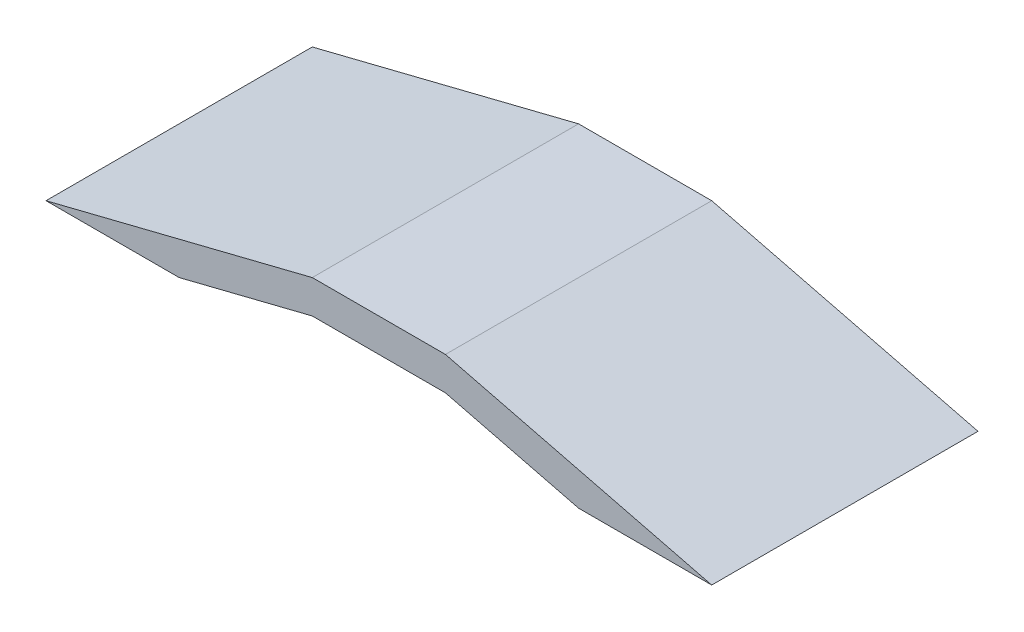
SolidWorks part; units mm, degrees
ref_plane "Front Plane" through (0, 0, 0) normal (0, 0, 1) x (1, 0, 0)
ref_plane "Top Plane" through (0, 0, 0) normal (0, 1, 0) x (1, 0, 0)
ref_plane "Right Plane" through (0, 0, 0) normal (1, 0, 0) x (0, 0, -1)
sketch "Sketch1" plane through (0, 0, 0) normal (0, 0, 1) x (1, 0, 0)
  line L0 (0, 0) -> (2000, 0)
  line L1 (2000, 0) -> (0, 500)
  line L2 (0, 500) -> (0, 0)
  line L3 (-500, 500) -> (-500, 0) construction
  line L4 (0, 0) -> (-1000, 0)
  line L5 (0, 0) -> (0, 500)
  line L6 (0, 500) -> (-1000, 500)
  line L7 (-1000, 0) -> (-1000, 500)
  line L8 (-1000, 0) -> (-3000, 0)
  line L9 (-1000, 500) -> (-1000, 0)
  line L10 (-3000, 0) -> (-1000, 500)
  line L11 (-2000, 0) -> (-1000, 250)
  line L12 (-1000, 250) -> (0, 250)
  line L13 (0, 250) -> (1000, 0)
  dimension "D1" = 2000
  dimension "D2" = 500
  dimension "D3" = 1000
extrude "Boss-Extrude2" add sketch "Sketch1" against normal blind 2000 contours L8 L11 L9 L10 | L3 L6 L9 L12 | L6 L3 L12 L2 | L2 L13 L0 L1
